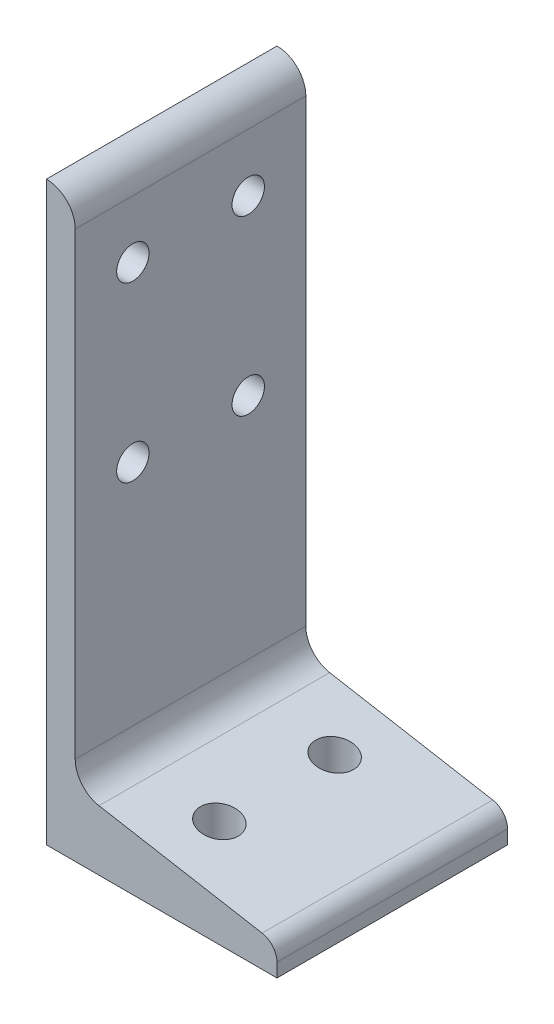
SolidWorks part; units mm, degrees
material "6061 Alloy"
ref_plane "Front Plane" through (0, 0, 0) normal (0, 0, 1) x (1, 0, 0)
ref_plane "Top Plane" through (0, 0, 0) normal (0, 1, 0) x (1, 0, 0)
ref_plane "Right Plane" through (0, 0, 0) normal (1, 0, 0) x (0, 0, -1)
sketch "Sketch1" plane through (0, 0, 0) normal (0, 0, 1) x (1, 0, 0)
  line L24 (6.6309, 23.8279) -> (-1.3066, 25.2275)
  line L25 (6.6309, 23.8279) -> (-1.3066, 25.2275)
  line L26 (6.6309, 13.699) -> (-1.3066, 13.699)
  line L27 (-16.3879, 79.9803) -> (-16.3879, 87.1177)
  line L28 (6.6309, 13.699) -> (-1.3066, 13.699)
  line L29 (-16.3879, 79.9803) -> (-16.3879, 87.1177)
  line L30 (-22.7379, 87.1177) -> (-22.7379, 79.9803)
  line L31 (-16.3879, 118.0803) -> (-16.3879, 125.2177)
  line L32 (-22.7379, 87.1177) -> (-22.7379, 79.9803)
  line L33 (-16.3879, 118.0803) -> (-16.3879, 125.2177)
  line L34 (-22.7379, 125.2177) -> (-22.7379, 118.0803)
  line L35 (24.7878, 20.6263) -> (-11.1406, 26.9615)
  line L36 (-22.7379, 125.2177) -> (-22.7379, 118.0803)
  line L37 (-22.7379, 13.699) -> (28.0621, 13.699)
  line L38 (24.7878, 20.6263) -> (-11.1406, 26.9615)
  line L39 (28.0621, 13.699) -> (28.0621, 16.7241)
  line L40 (28.0621, 13.699) -> (-22.7379, 13.699)
  line L41 (-22.7379, 140.699) -> (-22.7379, 13.699)
  line L42 (-16.3879, 33.215) -> (-16.3879, 134.349)
  line L43 (28.0621, 16.7241) -> (28.0621, 13.699)
  line L44 (-22.7379, 13.699) -> (-22.7379, 140.699)
  line L45 (-16.3879, 33.215) -> (-16.3879, 134.349)
  ellipse E0 centre (-10.0379, 33.215) end of major axis (-10.0379, 39.565) minor radius 6.35 (-16.3879, 33.215) -> (-11.1406, 26.9615) ccw
  ellipse E1 centre (24.0997, 16.7241) end of major axis (24.0997, 12.7617) minor radius 3.9624 (28.0621, 16.7241) -> (24.7878, 20.6263) ccw
  ellipse E2 centre (-22.7379, 134.349) end of major axis (-29.0879, 134.349) minor radius 6.35 (-16.3879, 134.349) -> (-22.7379, 140.699) ccw
  ellipse E3 centre (-10.0379, 33.215) end of major axis (-16.3879, 33.215) minor radius 6.35 (-16.3879, 33.215) -> (-11.1406, 26.9615) ccw
  ellipse E4 centre (24.0997, 16.7241) end of major axis (20.1373, 16.7241) minor radius 3.9624 (28.0621, 16.7241) -> (24.7878, 20.6263) ccw
  ellipse E5 centre (-22.7379, 134.349) end of major axis (-29.0879, 134.349) minor radius 6.35 (-16.3879, 134.349) -> (-22.7379, 140.699) ccw
extrude "Extrude1" add sketch "Sketch1" along normal blind 50.8 contours L42 E2 L41 L34 L30 L37 L26 L39 E1 L35 L24 E0 L27 L31
sketch "Sketch2" plane through (-16.3879, 0, 0) normal (1, 0, 0) x (0, 0, -1)
  circle A0 centre (-38.1, 121.649) radius 3.5687
  circle A1 centre (-38.1, 83.549) radius 3.5687
  circle A2 centre (-12.6852, 83.549) radius 3.5687
  circle A3 centre (-12.6852, 121.649) radius 3.5687
extrude "Cut-Extrude1" cut sketch "Sketch2" against normal through all
sketch "Sketch3" plane through (0, 13.699, 0) normal (0, -1, 0) x (1, 0, 0)
  circle A0 centre (2.6621, 12.7) radius 4.1656
  circle A1 centre (2.6621, 38.1) radius 4.1656
  dimension "D1" = 8.3312
  dimension "D2" = 8.3312
extrude "Cut-Extrude2" cut sketch "Sketch3" against normal through all
